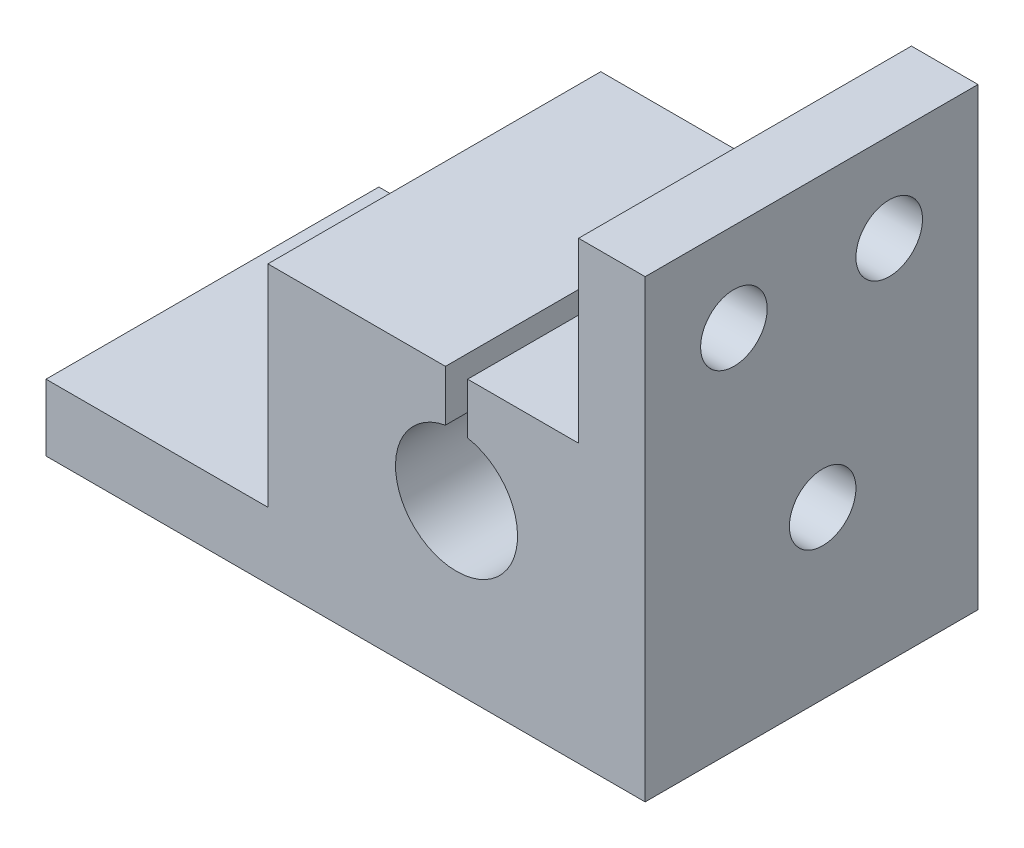
SolidWorks part; units mm, degrees
ref_plane "Front Plane" through (0, 0, 0) normal (0, 0, 1) x (1, 0, 0)
ref_plane "Top Plane" through (0, 0, 0) normal (0, 1, 0) x (1, 0, 0)
ref_plane "Right Plane" through (0, 0, 0) normal (1, 0, 0) x (0, 0, -1)
sketch "Croquis1" plane through (0, 0, 0) normal (0, 1, 0) x (1, 0, 0)
  line L1 (-20, 7.5) -> (20, 7.5)
  line L2 (-20, 7.5) -> (-20, -7.5)
  line L3 (-20, -7.5) -> (20, -7.5)
  line L4 (20, 7.5) -> (20, -7.5)
  line L5 (-20, 7.5) -> (20, -7.5) construction
  line L6 (-20, -7.5) -> (20, 7.5) construction
  line L7 (-8.5, -7.5) -> (8.5, -7.5)
  line L8 (-8.5, -7.5) -> (-8.5, 7.5)
  line L9 (-8.5, 7.5) -> (8.5, 7.5)
  line L10 (8.5, -7.5) -> (8.5, 7.5)
  line L11 (-8.5, -7.5) -> (8.5, 7.5) construction
  line L12 (-8.5, 7.5) -> (8.5, -7.5) construction
  point P0 (0, 0)
  point P7 (0, 0)
  dimension "D1" = 40
  dimension "D2" = 15
  dimension "D3" = 17
  dimension "D4" = 15
extrude "Saliente-Extruir1" add sketch "Croquis1" along normal blind 12.5 contours L3 L10 L1 L8
sketch "Croquis2" plane through (0, 0, -7.5) normal (0, 0, -1) x (-1, 0, 0)
  line L0 (8.5, 0) -> (-8.5, 0) construction
  line L1 (-0.5, 12.5) -> (-0.5, 10.2042)
  line L2 (8.5, 12.5) -> (-8.5, 12.5) construction
  line L3 (0, 12.5) -> (0, 31.0218) construction
  line L4 (0.5, 12.5) -> (0.5, 10.2042)
  circle A0 centre (0, 7.5) radius 2.75
  dimension "D1" = 5.5
  dimension "D2" = 7.5
  dimension "D3" = 0.5
extrude "Cortar-Extruir1" cut sketch "Croquis2" against normal blind 20
sketch "Croquis4" plane through (-8.5, 0, 0) normal (-1, 0, 0) x (0, 0, 1)
  line L0 (-7.5, 12.5) -> (-7.5, 0) construction
  line L2 (7.5, 0) -> (-7.5, 0) construction
  circle A0 centre (-0.5, 7.5) radius 1.5
  dimension "D1" = 3
  dimension "D2" = 7
  dimension "D3" = 7.5
extrude "Cortar-Extruir3" cut sketch "Croquis4" against normal blind 20
sketch "Croquis8" plane through (-8.5, 0, 0) normal (-1, 0, 0) x (0, 0, 1)
  line L0 (7.5, 0) -> (7.5, 3)
  line L1 (7.5, 12.5) -> (7.5, 0) construction
  line L2 (7.5, 3) -> (-7.5, 3)
  line L3 (-7.5, 3) -> (-7.5, 0)
  line L4 (-7.5, 0) -> (7.5, 0)
  line L5 (-7.5, 12.5) -> (-7.5, 0) construction
  dimension "D1" = 3
extrude "Saliente-Extruir2" add sketch "Croquis8" along normal blind 10
sketch "Croquis9" plane through (0, 3, 0) normal (0, 1, 0) x (1, 0, 0)
  line L0 (-18.5, -7.5) -> (-18.5, 7.5) construction
  line L1 (-18.5, -7.5) -> (-8.5, -7.5) construction
  circle A0 centre (-13.5, 0) radius 1.5
  dimension "D1" = 5
  dimension "D2" = 7.5
  dimension "D3" = 3
extrude "Cortar-Extruir6" cut sketch "Croquis9" against normal blind 6
sketch "Croquis10" plane through (0, 12.5, 0) normal (0, 1, 0) x (1, 0, 0)
  line L0 (8.5, -7.5) -> (5.5, -7.5)
  line L2 (5.5, -7.5) -> (5.5, 7.5)
  line L4 (5.5, 7.5) -> (8.5, 7.5)
  line L5 (8.5, 7.5) -> (8.5, -7.5)
  point P3 (0, 0)
  point P4 (0, 0)
  point P5 (0, 0)
  point P11 (0, 0)
  dimension "D1" = 3
extrude "Saliente-Extruir3" add sketch "Croquis10" along normal blind 8
sketch "Croquis11" plane through (5.5, 0, 0) normal (-1, 0, 0) x (0, 0, 1)
  line L0 (-7.5, 20.5) -> (7.5, 20.5) construction
  line L1 (7.5, 20.5) -> (7.5, 12.5) construction
  line L2 (-7.5, 20.5) -> (-7.5, 12.5) construction
  circle A0 centre (3.5, 16.5) radius 1.5
  circle A1 centre (-3.5, 16.5) radius 1.5
  dimension "D2" = 3
  dimension "D3" = 3
  dimension "D6" = 4
  dimension "D1" = 4
  dimension "D4" = 4
  dimension "D5" = 4
extrude "Cortar-Extruir8" cut sketch "Croquis11" against normal blind 6
